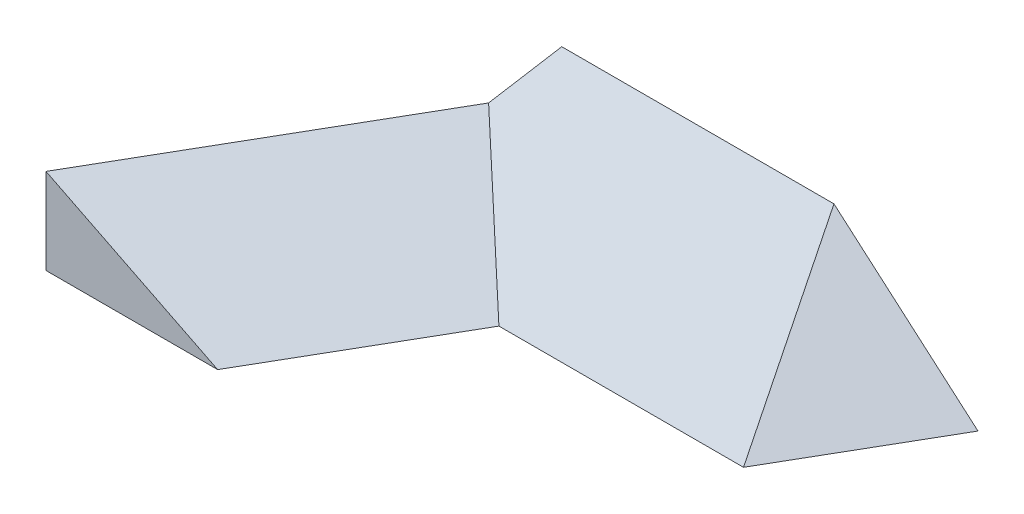
SolidWorks part; units mm, degrees
ref_plane "Front" through (0, 0, 0) normal (0, 0, 1) x (1, 0, 0)
ref_plane "Top" through (0, 0, 0) normal (0, 1, 0) x (1, 0, 0)
ref_plane "Right" through (0, 0, 0) normal (1, 0, 0) x (0, 0, -1)
sketch "Sketch1" plane through (0, 0, 0) normal (1, 0, 0) x (0, 0, -1)
  line L0 (0, 0) -> (0, 41.955)
  line L1 (0, 41.955) -> (-50, 0)
  line L2 (-50, 0) -> (0, 0)
  dimension "D1" = 50
  dimension "D2" = 40
extrude "Extrude1" add sketch "Sketch1" against normal blind 153.73
sketch "Sketch2" plane through (0, 0, 0) normal (0, 1, 0) x (1, 0, 0)
  line L0 (-140, 0) -> (-203.5085, -110)
  line L1 (-153.73, -50) -> (0, -50) construction
  line L2 (-96.6987, -25) -> (-160.2073, -135)
  line L3 (-111.1325, -50) -> (-111.1325, -87.3854) construction
  line L4 (-140, 0) -> (-96.6987, -25)
  line L5 (-203.5085, -110) -> (-145.7735, -110)
  line L6 (-96.6987, -25) -> (-160.2073, -135) construction
  line L7 (-203.5085, -110) -> (-160.2073, -135)
  dimension "D1" = 120
  dimension "D2" = 110
  dimension "D3" = 111.1325
ref_plane "Plane2" through (0, 0, 110) normal (0, 0, 1) x (1, 0, 0)
sketch "Sketch3" plane through (0, 0, 110) normal (0, 0, 1) x (1, 0, 0)
  point P0 (-203.5085, 32.0162)
ref_plane "Plane3" through (-98.5085, 0, 170.6218) normal (-0.5, 0, 0.866) x (0.866, 0, 0.5)
sketch "Sketch4" plane through (-98.5085, 0, 170.6218) normal (-0.5, 0, 0.866) x (0.866, 0, 0.5)
  line L2 (-121.2436, 28.8675) -> (-71.2436, 0)
  line L3 (-71.2436, 0) -> (-121.2436, 0)
  line L7 (-121.2436, 0) -> (-121.2436, 28.8675)
  dimension "D1" = 30
extrude "Extrude2" add sketch "Sketch4" against normal blind 127.02
sketch "Sketch5" plane through (0, 0, 0) normal (0, 1, 0) x (1, 0, 0)
  line L0 (-153.7277, -23.777) -> (0, -23.777) construction
  line L1 (0, 0) -> (0, -50) construction
  line L2 (-140, 0) -> (-203.5085, -110) construction
sketch "Sketch6" plane through (0, 0, 0) normal (0, 1, 0) x (1, 0, 0)
  line L0 (-161.0488, -36.4575) -> (-140, 0)
  line L1 (-140, 0) -> (-203.5085, -110) construction
  line L2 (-140, 0) -> (-161.0488, 0)
  line L3 (-161.0488, 0) -> (-161.0488, -36.4575)
extrude "Cut-Extrude1" cut sketch "Sketch6" along normal through all
sketch "Sketch7" plane through (0, 0, 0) normal (0, 1, 0) x (1, 0, 0)
  line L0 (0, 0) -> (-28.8675, -50) construction
  line L1 (-111.1325, -50) -> (0, -50) construction
  dimension "D1" = 60
ref_plane "Plane5" through (-28.8675, 0, 50) normal (-0.5, 0, 0.866) x (0.866, 0, 0.5)
sketch "Sketch9" plane through (-28.8675, 0, 50) normal (-0.5, 0, 0.866) x (0.866, 0, 0.5)
  line L2 (33.2939, 48.6756) -> (33.2939, 0)
  line L3 (33.2939, 0) -> (0, 0)
  line L4 (0, 0) -> (-48.6756, 48.6756)
  line L5 (-71.2436, 0) -> (25, 0) construction
  line L6 (-48.6756, 48.6756) -> (33.2939, 48.6756)
  dimension "D1" = 45
extrude "Cut-Extrude2" cut sketch "Sketch9" against normal blind 60 and the other way blind 40
sketch "Sketch10" plane through (0, 0, 0) normal (0, 1, 0) x (1, 0, 0)
  line L0 (-203.8407, -109.9744) -> (-143.7473, -109.9744)
  line L1 (-143.7473, -109.9744) -> (-143.7473, -138.6938)
  line L2 (-143.7473, -138.6938) -> (-203.8407, -138.6938)
  line L3 (-203.8407, -138.6938) -> (-203.8407, -109.9744)
extrude "Cut-Extrude3" cut sketch "Sketch10" along normal through all
ref_plane "BC Dihedral Angle Plane" through (-38.6565, 20.9775, 25) normal (0.2873, -0.6157, 0.7337) x (0.9578, 0.1847, -0.2201)
